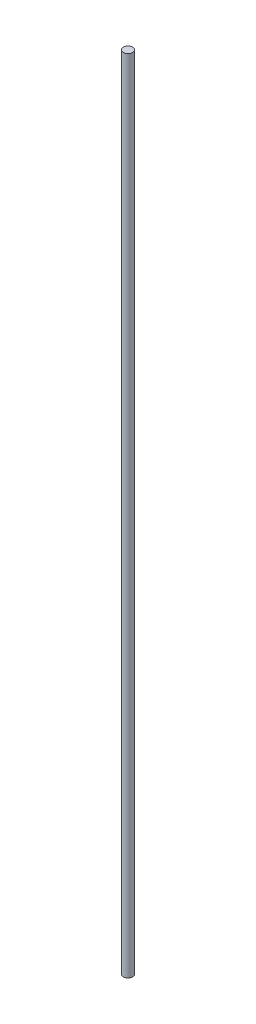
SolidWorks part; units mm, degrees
ref_plane "Alzado" through (0, 0, 0) normal (0, 0, 1) x (1, 0, 0)
ref_plane "Planta" through (0, 0, 0) normal (0, 1, 0) x (1, 0, 0)
ref_plane "Vista lateral" through (0, 0, 0) normal (1, 0, 0) x (0, 0, -1)
sketch "Croquis2" plane through (0, 0, 0) normal (0, 1, 0) x (1, 0, 0)
  circle A0 centre (0, 0) radius 0.875
  dimension "D1" = 1.75
extrude "Saliente-Extruir1" add sketch "Croquis2" along normal blind 150
